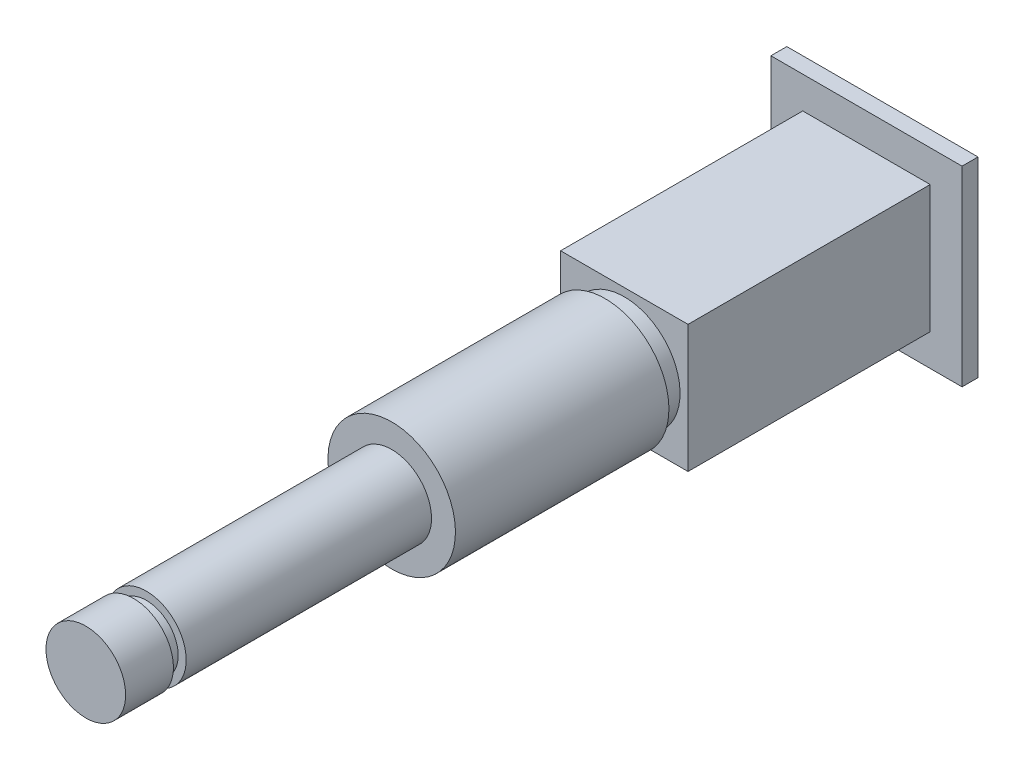
SolidWorks part; units mm, degrees
ref_plane "Front Plane" through (0, 0, 0) normal (0, 0, 1) x (1, 0, 0)
ref_plane "Top Plane" through (0, 0, 0) normal (0, 1, 0) x (1, 0, 0)
ref_plane "Right Plane" through (0, 0, 0) normal (1, 0, 0) x (0, 0, -1)
sketch "Sketch1" plane through (0, 0, 0) normal (1, 0, 0) x (0, 0, -1)
  line L0 (55, 0) -> (-55, 0) construction
  line L1 (-19.2, 0) -> (30.8, 0)
  line L2 (-19.2, 0) -> (-19.2, 2.5)
  line L3 (-19.2, 2.5) -> (-16.2, 2.5)
  line L5 (0, -11.3439) -> (0, 19.3783) construction
  line L6 (0, 55) -> (0, -55) construction
  line L7 (-15.4, 2.5) -> (-15.4, 2)
  line L8 (-15.4, 2) -> (-16.2, 2)
  line L9 (-16.2, 2) -> (-16.2, 2.5)
  line L10 (0, 4) -> (13.4, 4)
  line L15 (29.8, 4) -> (29.8, 5)
  line L16 (29.8, 5) -> (30.8, 5)
  line L17 (30.8, 5) -> (30.8, 0)
  line L18 (-15.4, 2.5) -> (0, 2.5)
  line L19 (0, 2.5) -> (0, 4)
  line L20 (14.6, 4) -> (14.6, 3.5)
  line L21 (14.6, 3.5) -> (13.4, 3.5)
  line L22 (13.4, 3.5) -> (13.4, 4)
  line L23 (14.6, 4) -> (29.8, 4)
  dimension "D1" = 50
  dimension "D2" = 2.5
  dimension "D3" = 3.8
  dimension "D4" = 0.5
  dimension "D5" = 0.8
  dimension "D6" = 1
  dimension "D7" = 5
  dimension "D8" = 4
  dimension "D9" = 15.4
  dimension "D10" = 16.2
  dimension "D11" = 3.5
  dimension "D12" = 1.2
revolve "Revolve1" add sketch "Sketch1" angle 360 about L1
sketch "Sketch3" plane through (0, 0, -29.8) normal (0, 0, 1) x (1, 0, 0)
  line L1 (4, -4) -> (-4, -4)
  line L2 (4, -4) -> (4, 4)
  line L3 (4, 4) -> (-4, 4)
  line L4 (-4, -4) -> (-4, 4)
  line L5 (4, -4) -> (-4, 4) construction
  line L6 (4, 4) -> (-4, -4) construction
  point P0 (0, 0)
  dimension "D1" = 8
extrude "Boss-Extrude2" add sketch "Sketch3" along normal up to surface (15.2 mm away) up to face at (0, -3.5, -14.6)
sketch "Sketch4" plane through (0, 0, -30.8) normal (0, 0, -1) x (-1, 0, 0)
  line L1 (6, -6) -> (-6, -6)
  line L2 (6, -6) -> (6, 6)
  line L3 (6, 6) -> (-6, 6)
  line L4 (-6, -6) -> (-6, 6)
  line L5 (6, -6) -> (-6, 6) construction
  line L6 (6, 6) -> (-6, -6) construction
  point P0 (0, 0)
  dimension "D1" = 12
extrude "Boss-Extrude3" add sketch "Sketch4" against normal up to surface (1 mm away) up to face at (0, 4.5, -29.8)
